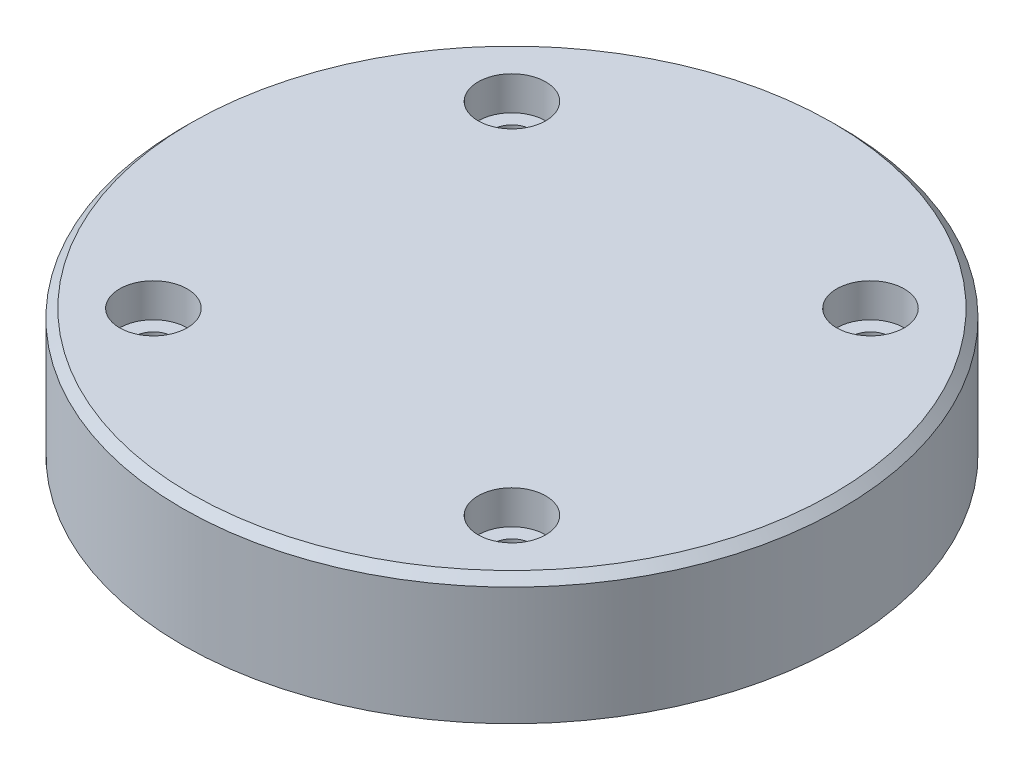
SolidWorks part; units mm, degrees
ref_plane "Front" through (0, 0, 0) normal (0, 0, 1) x (1, 0, 0)
ref_plane "Top" through (0, 0, 0) normal (0, 1, 0) x (1, 0, 0)
ref_plane "Right" through (0, 0, 0) normal (1, 0, 0) x (0, 0, -1)
sketch "Sketch1" plane through (0, 0, 0) normal (0, 1, 0) x (1, 0, 0)
  circle A0 centre (0, 0) radius 39
  dimension "D1" = 78
extrude "Boss-Extrude1" add sketch "Sketch1" along normal blind 15
hole_wizard "CBORE for M4 Socket Head Cap Screw1" positions "Sketch3" profile "Sketch2" counterbore size "M4" standard "JIS" end condition through all
sketch "Sketch3" plane through (0, 15, 0) normal (0, 1, 0) x (-1, 0, 0)
  line L0 (-48.6827, 0) -> (44.7355, 0) construction
  line L3 (0, 40.94) -> (0, -41.9521) construction
  line L6 (-34.6775, -34.6775) -> (44.8942, 44.8942) construction
  line L7 (-33.039, 33.039) -> (34.9758, -34.9758) construction
  circle A0 centre (0, 0) radius 30 construction
  point P0 (21.2132, -21.2132)
  point P1 (21.2132, 21.2132)
  point P3 (-21.2132, 21.2132)
  point P5 (-21.2132, -21.2132)
  dimension "D3" = 60
  dimension "D1" = 45
  dimension "D2" = 45
sketch "Sketch2" plane through (-21.2132, 15, -21.2132) normal (1, 0, 0) x (0, 0, 1)
  line L0 (0, 0) -> (0, 15)
  line L1 (0, 15) -> (2.25, 15)
  line L3 (2.25, 15) -> (2.25, 4)
  line L4 (2.25, 4) -> (4, 4)
  line L5 (4, 4) -> (4, 0)
  line L7 (4, 0) -> (0, 0)
  line L11 (0, -6.35) -> (0, 107.95) construction
  dimension "通し穴の直径" = 4.5
  dimension "通し穴の深さ" = 15
  dimension "座ぐり穴の直径" = 8
  dimension "座ぐり穴の深さ" = 4
chamfer "Chamfer1" distance 1 angle 45 1 edges at (0, 15, 39)
